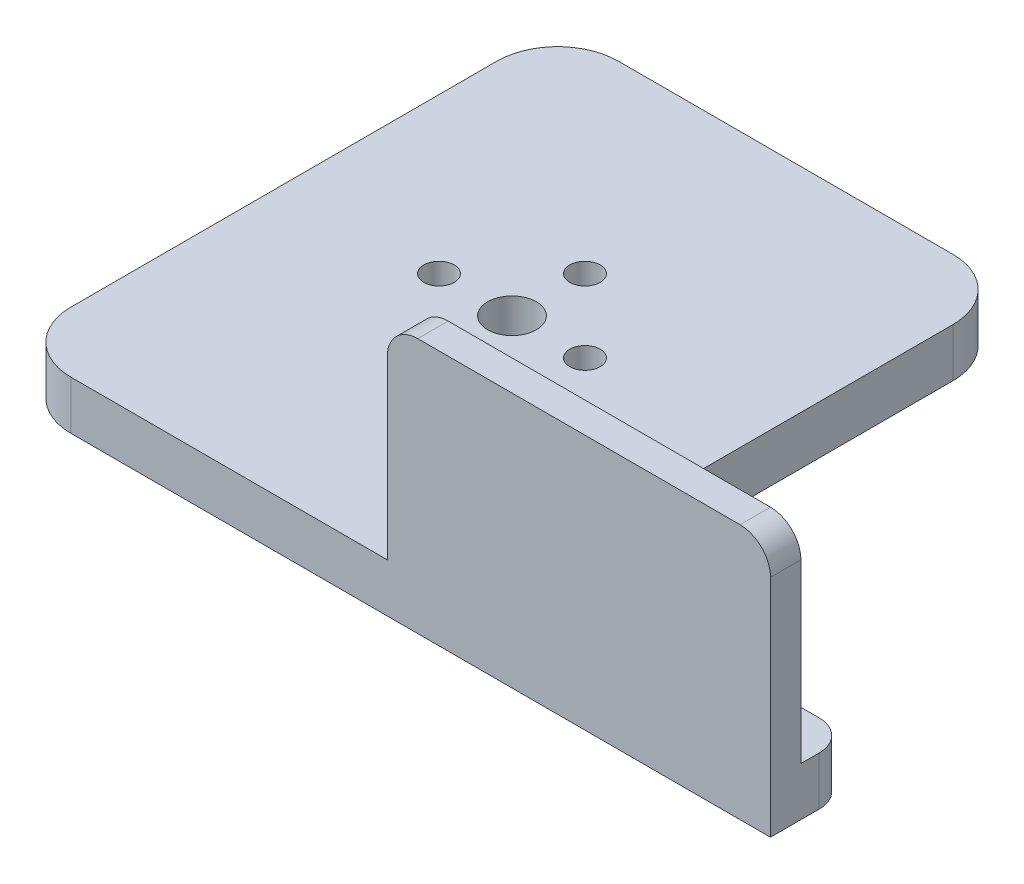
SolidWorks part; units mm, degrees
ref_plane "Front Plane" through (0, 0, 0) normal (0, 0, 1) x (1, 0, 0)
ref_plane "Top Plane" through (0, 0, 0) normal (0, 1, 0) x (1, 0, 0)
ref_plane "Right Plane" through (0, 0, 0) normal (1, 0, 0) x (0, 0, -1)
sketch "Sketch1" plane through (0, 0, 0) normal (0, 1, 0) x (1, 0, 0)
  line L1 (0, 0) -> (75, 0)
  line L2 (0, 0) -> (0, -90)
  line L3 (0, -90) -> (75, -90)
  line L4 (75, 0) -> (75, -90)
  line L5 (75, -90) -> (125, -90)
  line L6 (75, -90) -> (75, -77)
  line L7 (75, -77) -> (125, -77)
  line L8 (125, -90) -> (125, -77)
  dimension "D1" = 90
  dimension "D2" = 75
  dimension "D3" = 50
  dimension "D4" = 13
extrude "Boss-Extrude1" add sketch "Sketch1" along normal blind 8 contours L4 L1 L2 L3 | L5 L8 L7 L4
sketch "Sketch2" plane through (0, 0, 0) normal (0, -1, 0) x (1, 0, 0)
  line L0 (37.5, 0) -> (37.5, 90) construction
  line L1 (0, 0) -> (75, 0) construction
  line L2 (0, 90) -> (125, 90) construction
  circle A0 centre (37.5, 45) radius 16
fillet "Fillet2" radius 10 1 edges at (0, 4, 0)
fillet "Fillet3" radius 10 1 edges at (0, 4, 90)
fillet "Fillet4" radius 10 1 edges at (75, 4, 0)
sketch "Sketch7" plane through (125, 0, 0) normal (1, 0, 0) x (0, 0, -1)
  line L1 (-90, 8) -> (-85, 8)
  line L2 (-90, 8) -> (-90, 42)
  line L3 (-90, 42) -> (-85, 42)
  line L4 (-85, 8) -> (-85, 42)
  dimension "D1" = 34
  dimension "D2" = 5
extrude "Boss-Extrude3" add sketch "Sketch7" against normal blind 63
fillet "Fillet5" radius 5 1 edges at (125, 42, 87.5)
fillet "Fillet6" radius 5 1 edges at (125, 4, 77)
fillet "Fillet7" radius 5 1 edges at (62, 42, 87.5)
extrude "Cut-Extrude1" cut sketch "Sketch2" against normal blind 1 contours A0
sketch "Sketch8" plane through (0, 1, 0) normal (0, -1, 0) x (1, 0, 0)
  line L0 (37.5, 45) -> (37.5, 57)
  circle A0 centre (37.5, 45) radius 4
  circle A1 centre (37.5, 57) radius 2.5
  circle A2 centre (49.5, 45) radius 2.5
  circle A3 centre (37.5, 33) radius 2.5
  circle A4 centre (25.5, 45) radius 2.5
  dimension "D1" = 4
extrude "Cut-Extrude2" cut sketch "Sketch8" against normal up to next
